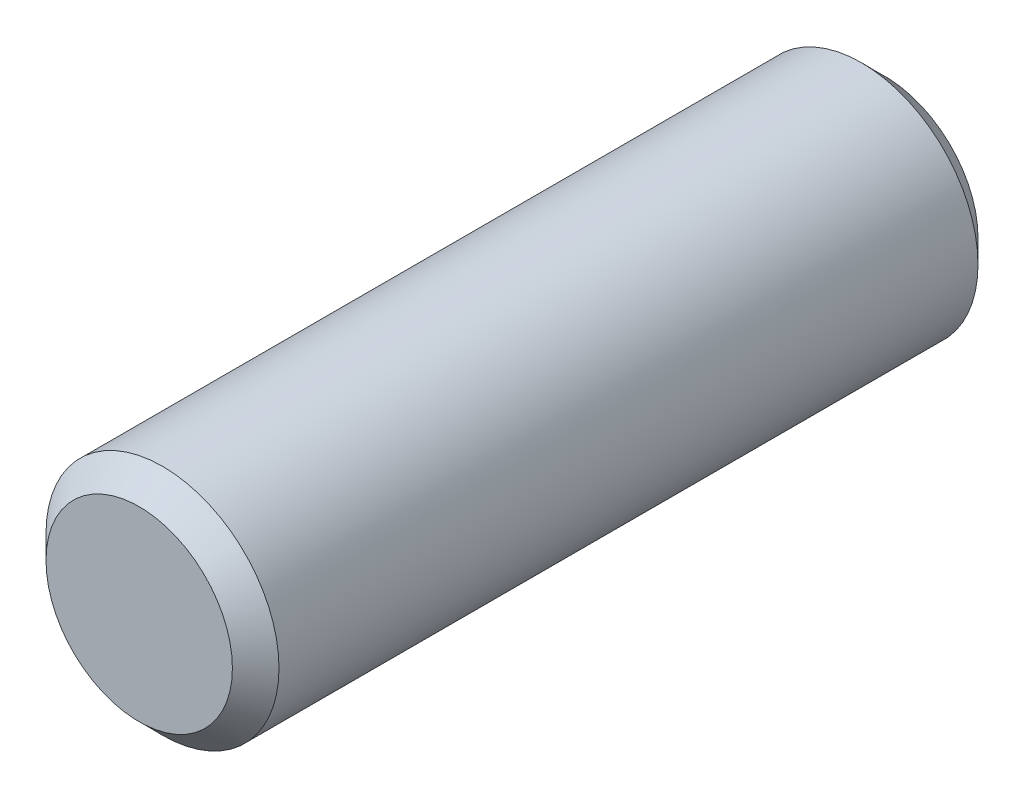
SolidWorks part; units mm, degrees
material "1.4310 (X10CrNi18-8)"
ref_plane "Front Plane" through (0, 0, 0) normal (0, 0, 1) x (1, 0, 0)
ref_plane "Top Plane" through (0, 0, 0) normal (0, 1, 0) x (1, 0, 0)
ref_plane "Right Plane" through (0, 0, 0) normal (1, 0, 0) x (0, 0, -1)
sketch "Sketch1" plane through (0, 0, 0) normal (0, 0, 1) x (1, 0, 0)
  circle A0 centre (0, 0) radius 2.5
  dimension "D1" = 5
extrude "Boss-Extrude1" add sketch "Sketch1" along normal mid plane 16
chamfer "Chamfer1" distance 0.5 angle 45 2 edges at (2.5, 0, -8) (2.5, 0, 8)
